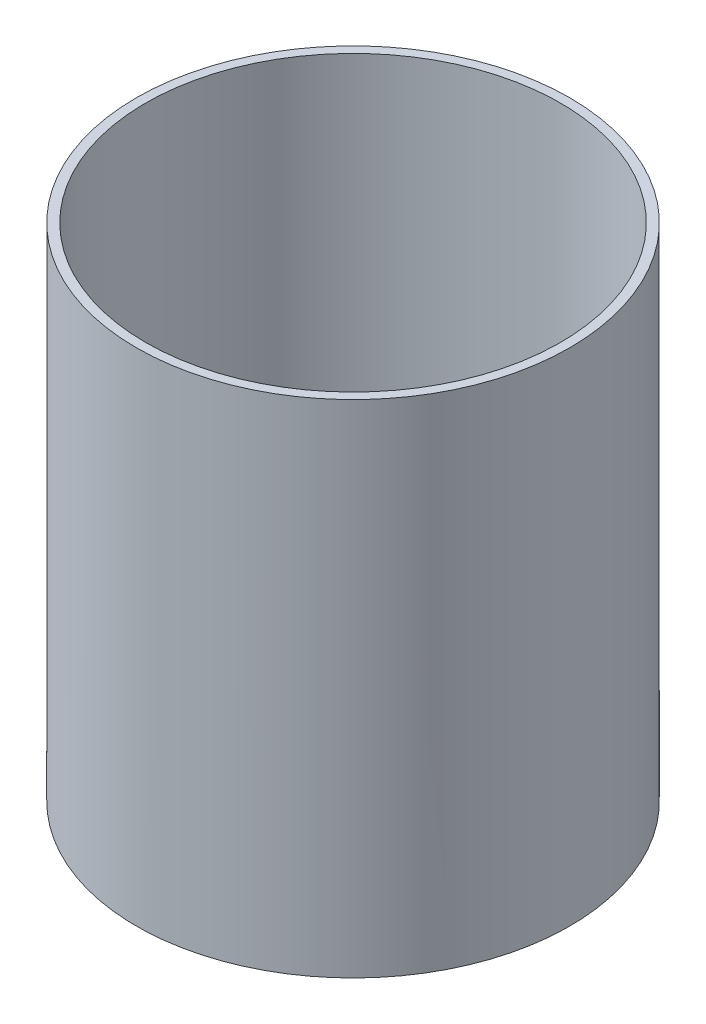
SolidWorks part; units mm, degrees
ref_plane "Front Plane" through (0, 0, 0) normal (0, 0, 1) x (1, 0, 0)
ref_plane "Top Plane" through (0, 0, 0) normal (0, 1, 0) x (1, 0, 0)
ref_plane "Right Plane" through (0, 0, 0) normal (1, 0, 0) x (0, 0, -1)
sketch "Sketch1" plane through (0, 0, 0) normal (0, 1, 0) x (1, 0, 0)
  circle A0 centre (0, 0) radius 48.641
  circle A1 centre (0, 0) radius 50.8
  dimension "D1" = 97.282
  dimension "D2" = 101.6
extrude "Boss-Extrude1" add sketch "Sketch1" along normal blind 114.3
sketch "Sketch2" plane through (0, 0, 0) normal (0, -1, 0) x (1, 0, 0)
  circle A0 centre (-38.1, 0) radius 3.175
  circle A1 centre (38.1, 0) radius 3.175
  circle M1 centre (0, 0) radius 50.8
  circle M2 centre (0, 0) radius 48.641
  dimension "D1" = 76.2
  dimension "D3" = 6.35
  dimension "D4" = 6.35
  dimension "D2" = 38.1
extrude "Boss-Extrude2" add sketch "Sketch2" along normal blind 3.175 contours A1 A0 M2 | M1 M2
